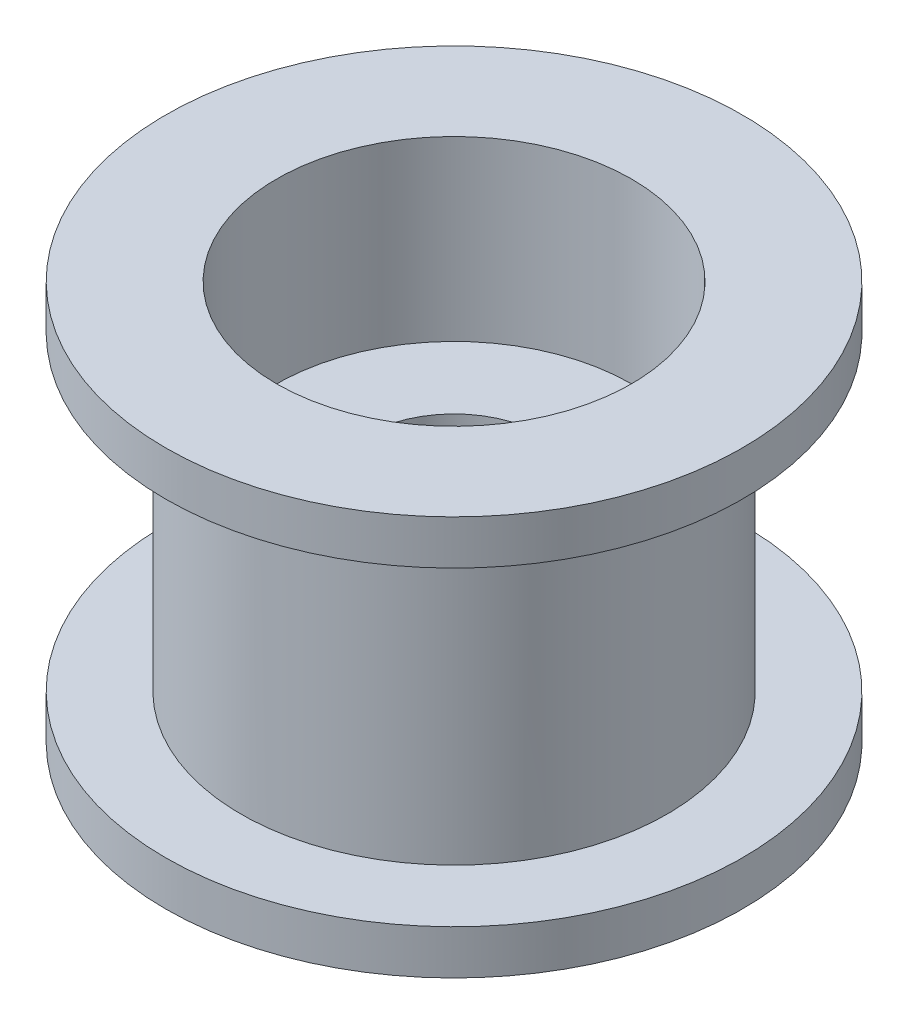
SolidWorks part; units mm, degrees
material "6061 Alloy"
ref_plane "Front Plane" through (0, 0, 0) normal (0, 0, 1) x (1, 0, 0)
ref_plane "Top Plane" through (0, 0, 0) normal (0, 1, 0) x (1, 0, 0)
ref_plane "Right Plane" through (0, 0, 0) normal (1, 0, 0) x (0, 0, -1)
sketch "Sketch2" plane through (0, 0, 0) normal (0, 1, 0) x (1, 0, 0)
  circle A0 centre (0, 0) radius 4.8
  dimension "D1" = 9.6
extrude "Boss-Extrude1" add sketch "Sketch2" along normal mid plane 7
sketch "Sketch3" plane through (0, 3.5, 0) normal (0, 1, 0) x (1, 0, 0)
  circle A0 centre (0, 0) radius 6.5
  dimension "D1" = 13
extrude "Boss-Extrude2" add sketch "Sketch3" along normal blind 1
sketch "Sketch4" plane through (0, 4.5, 0) normal (0, 1, 0) x (1, 0, 0)
  circle A0 centre (0, 0) radius 4
  dimension "D1" = 8
extrude "Cut-Extrude1" cut sketch "Sketch4" against normal blind 4
mirror "Mirror1" about plane through (0, 0, 0) normal (0, 1, 0) of "Cut-Extrude1", "Boss-Extrude2"
sketch "Sketch5" plane through (0, 0.5, 0) normal (0, 1, 0) x (1, 0, 0)
  circle A0 centre (0, 0) radius 2
  dimension "D1" = 4
extrude "Cut-Extrude2" cut sketch "Sketch5" against normal through all
